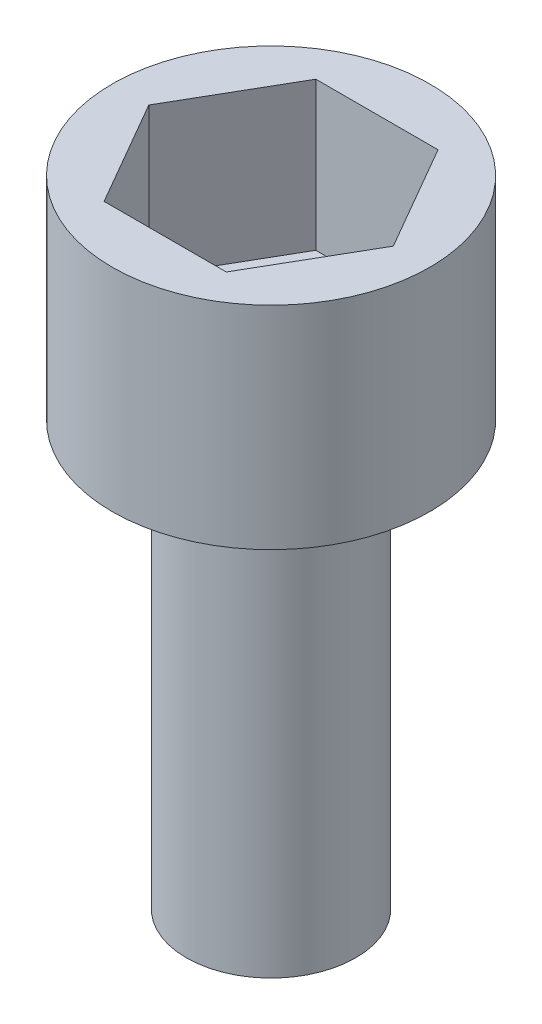
SolidWorks part; units mm, degrees
ref_plane "Front Plane" through (0, 0, 0) normal (0, 0, 1) x (1, 0, 0)
ref_plane "Top Plane" through (0, 0, 0) normal (0, 1, 0) x (1, 0, 0)
ref_plane "Right Plane" through (0, 0, 0) normal (1, 0, 0) x (0, 0, -1)
sketch "Sketch1" plane through (0, 0, 0) normal (0, 1, 0) x (1, 0, 0)
  circle A0 centre (0, 0) radius 4
  dimension "D1" = 8
extrude "Boss-Extrude1" add sketch "Sketch1" along normal blind 20
sketch "Sketch2" plane through (0, 20, 0) normal (0, 1, 0) x (1, 0, 0)
  circle A0 centre (0, 0) radius 7.5
  dimension "D1" = 15
extrude "Boss-Extrude2" add sketch "Sketch2" along normal blind 3
sketch "Sketch3" plane through (0, 23, 0) normal (0, 1, 0) x (1, 0, 0)
  line L1 (5.7735, 0) -> (2.8868, 5)
  line L2 (2.8868, 5) -> (-2.8868, 5)
  line L3 (-2.8868, 5) -> (-5.7735, 0)
  line L4 (-5.7735, 0) -> (-2.8868, -5)
  line L5 (-2.8868, -5) -> (2.8868, -5)
  line L6 (2.8868, -5) -> (5.7735, 0)
  circle A0 centre (0, 0) radius 5 construction
  circle A2 centre (0, 0) radius 7.5
  circle A3 centre (0, 0) radius 7.5
  point P1 (0, 0)
  dimension "D1" = 10
  dimension "D2" = 0
extrude "Boss-Extrude3" add sketch "Sketch3" along normal blind 7
